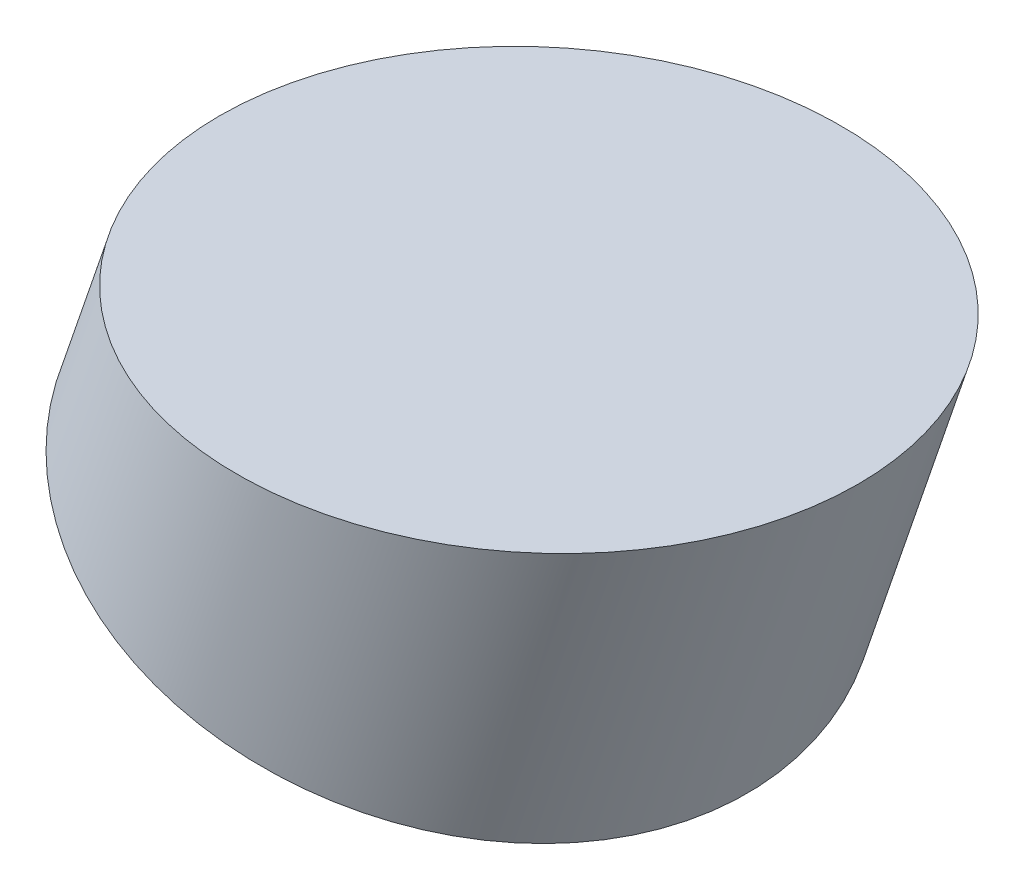
SolidWorks part; units mm, degrees
ref_plane "Plan de face" through (0, 0, 0) normal (0, 0, 1) x (1, 0, 0)
ref_plane "Plan de dessus" through (0, 0, 0) normal (0, 1, 0) x (1, 0, 0)
ref_plane "Plan de droite" through (0, 0, 0) normal (1, 0, 0) x (0, 0, -1)
sketch "Esquisse3" plane through (2.8318, 8.2461, 0) normal (0.3248, 0.9458, 0) x (0.9458, -0.3248, 0)
  circle A0 centre (-0.1129, -34.5393) radius 9.65
extrude "Boss.-Extru.2" add sketch "Esquisse3" along normal blind 20 from offset 3
sketch "Esquisse4" plane through (0, 0, 45.0393) normal (0, 0, 1) x (1, 0, 0)
  line L1 (-7.416, 18.3225) -> (29.6336, 18.3225)
  line L2 (-7.416, 18.3225) -> (-7.416, 35.036)
  line L3 (-7.416, 35.036) -> (29.6336, 35.036)
  line L4 (29.6336, 18.3225) -> (29.6336, 35.036)
extrude "Enlèv. mat.-Extru.1" cut sketch "Esquisse4" against normal blind 25
